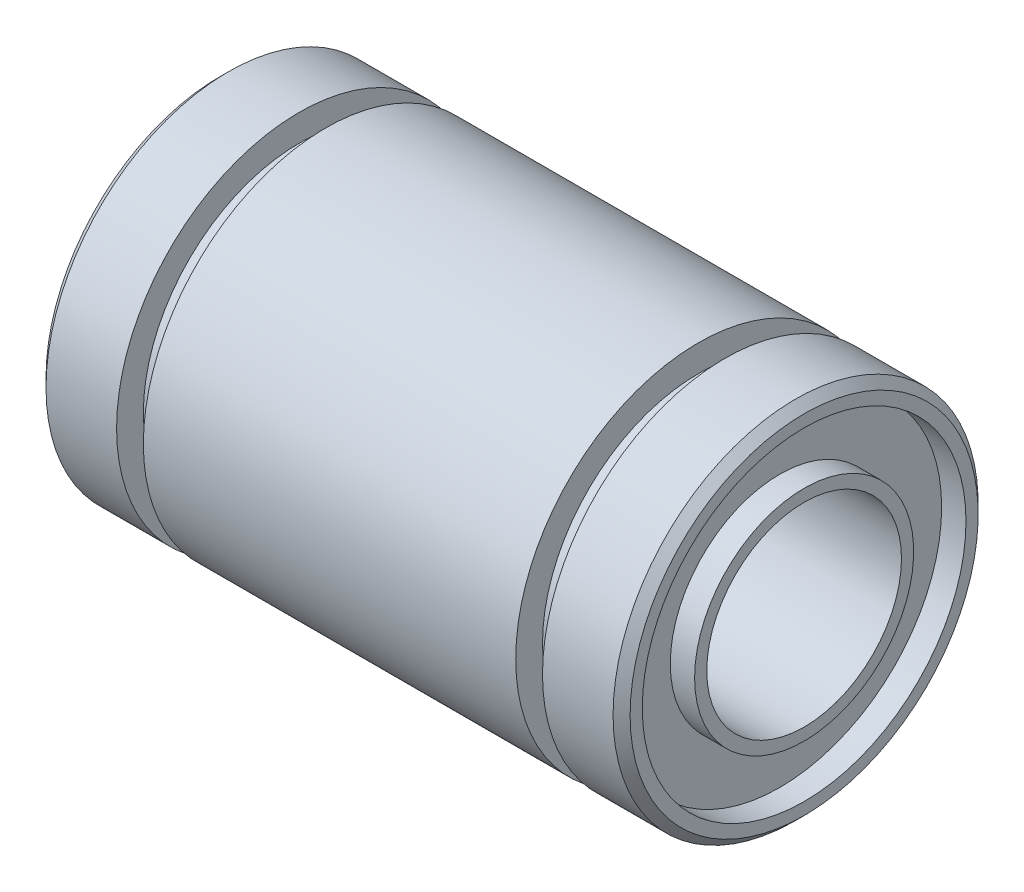
SolidWorks part; units mm, degrees
material "1060 Alloy"
ref_plane "Front Plane" through (0, 0, 0) normal (0, 0, 1) x (1, 0, 0)
ref_plane "Top Plane" through (0, 0, 0) normal (0, 1, 0) x (1, 0, 0)
ref_plane "Right Plane" through (0, 0, 0) normal (1, 0, 0) x (0, 0, -1)
sketch "Sketch1" plane through (0, 0, 0) normal (0, 0, 1) x (1, 0, 0)
  line L0 (-45.6895, 0) -> (45.6895, 0) construction
  line L1 (-11.65, 7.5) -> (-8.75, 7.5)
  line L2 (-8.75, 7.5) -> (-8.75, 6.4)
  line L3 (-8.75, 6.4) -> (-7.65, 6.4)
  line L4 (-7.65, 6.4) -> (-7.65, 7.5)
  line L5 (-7.65, 7.5) -> (7.65, 7.5)
  line L6 (0, 45.6895) -> (0, -45.6895) construction
  line L7 (-11.65, 7.5) -> (-12, 7.15)
  line L8 (-12, 7.15) -> (-12, 6.65)
  line L9 (-12, 6.65) -> (-11, 6.65)
  line L10 (-11, 6.65) -> (-11, 4.5)
  line L11 (-11, 4.5) -> (-12, 4.5)
  line L12 (-12, 4.5) -> (-12, 4)
  line L13 (-12, 4) -> (12, 4)
  line L14 (12, 4.5) -> (12, 4)
  line L15 (11, 4.5) -> (12, 4.5)
  line L16 (11, 6.65) -> (11, 4.5)
  line L17 (12, 6.65) -> (11, 6.65)
  line L18 (12, 7.15) -> (12, 6.65)
  line L19 (11.65, 7.5) -> (12, 7.15)
  line L20 (7.65, 6.4) -> (7.65, 7.5)
  line L21 (8.75, 6.4) -> (7.65, 6.4)
  line L22 (8.75, 7.5) -> (8.75, 6.4)
  line L23 (11.65, 7.5) -> (8.75, 7.5)
  point P19 (0, 4)
  point P26 (0, 7.5)
  dimension "D1" = 45
  dimension "D2" = 1.1
  dimension "D3" = 0.5
  dimension "L" = 19
  dimension "B" = 13.5
  dimension "W" = 1.1
  dimension "D" = 6
  dimension "D_1" = 5.75
  dimension "D4" = 0.5
  dimension "dr" = 3
  dimension "D5" = 1
revolve "Revolve1" add sketch "Sketch1" angle 360 about L0
equation "\"D\"=15"
equation "\"D1\"=14.3"
equation "\"dr\"=8"
equation "\"L\"=24"
equation "\"B\"=17.5"
equation "\"W\"=1.1"
equation "\"L@Sketch1\"= \"L\""
equation "\"B@Sketch1\"= \"B\""
equation "\"W@Sketch1\"= \"W\""
equation "\"dr@Sketch1\"= \"dr\" * 0.5"
equation "\"D@Sketch1\" = \"D\" * 0.5"
equation "\"D_1@Sketch1\" = \"D1\" * 0.5"
